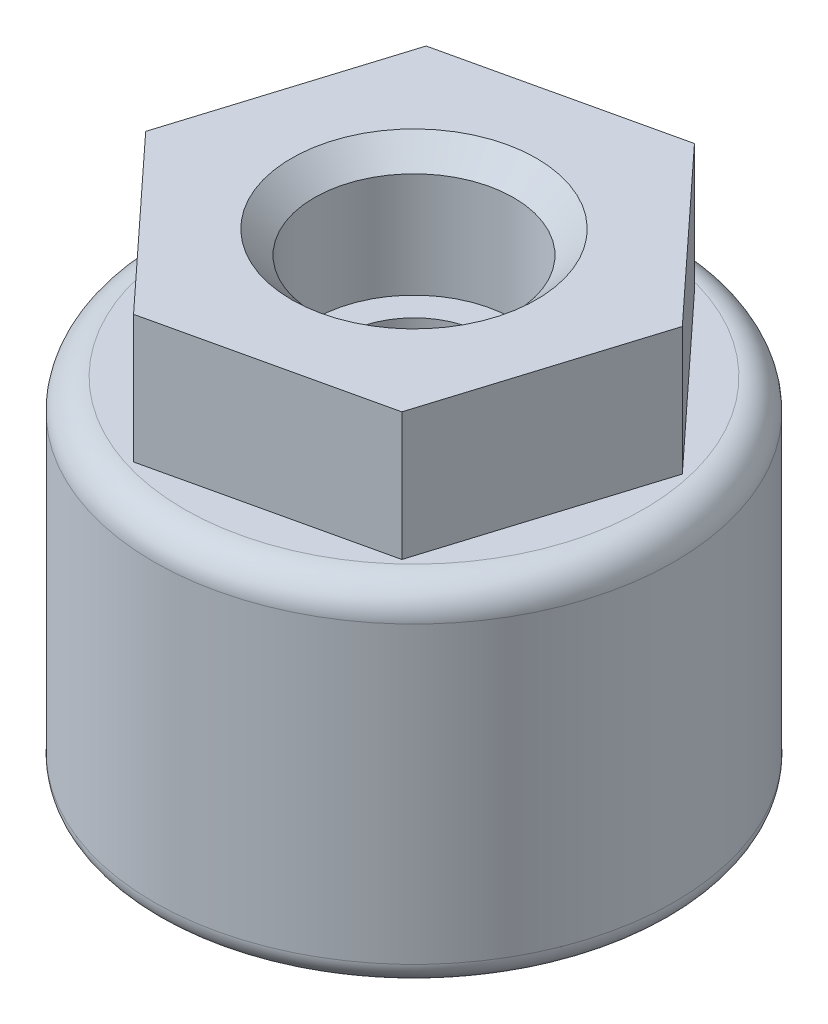
SolidWorks part; units mm, degrees
material "1023 Carbon Steel Sheet (SS)"
ref_plane "Front Plane" through (0, 0, 0) normal (0, 0, 1) x (1, 0, 0)
ref_plane "Top Plane" through (0, 0, 0) normal (0, 1, 0) x (1, 0, 0)
ref_plane "Right Plane" through (0, 0, 0) normal (1, 0, 0) x (0, 0, -1)
sketch "Sketch1" plane through (0, 0, 0) normal (0, 1, 0) x (1, 0, 0)
  circle A0 centre (0, 0) radius 14.285
extrude "Boss-Extrude1" add sketch "Sketch1" along normal blind 19.1
fillet "Radyus1" radius 1.67 1 edges at (0, 19.1, 14.285)
fillet "Radyus2" radius 1.25 1 edges at (0, 0, 14.285)
sketch "Sketch2" plane through (0, 19.1, 0) normal (0, 1, 0) x (1, 0, 0)
  line L1 (8.3643, -9.0306) -> (12.0029, 2.7284)
  line L2 (12.0029, 2.7284) -> (3.6386, 11.759)
  line L3 (3.6386, 11.759) -> (-8.3643, 9.0306)
  line L4 (-8.3643, 9.0306) -> (-12.0029, -2.7284)
  line L5 (-12.0029, -2.7284) -> (-3.6386, -11.759)
  line L6 (-3.6386, -11.759) -> (8.3643, -9.0306)
  circle A0 centre (0, 0) radius 10.66 construction
extrude "Boss-Extrude2" add sketch "Sketch2" along normal blind 7.02
sketch "Sketch4" plane through (0, 26.12, 0) normal (0, 1, 0) x (1, 0, 0)
  circle A0 centre (0, 0) radius 3.95
extrude "Cut-Extrude1" cut sketch "Sketch4" against normal blind 29.02 and the other way blind 2
sketch "Sketch5" plane through (0, 26.12, 0) normal (0, 1, 0) x (1, 0, 0)
  circle A0 centre (0, 0) radius 5.475
extrude "Cut-Extrude2" cut sketch "Sketch5" against normal blind 7.02
chamfer "Pah1" distance 1.25 angle 45 1 edges at (0, 26.12, 5.475)
